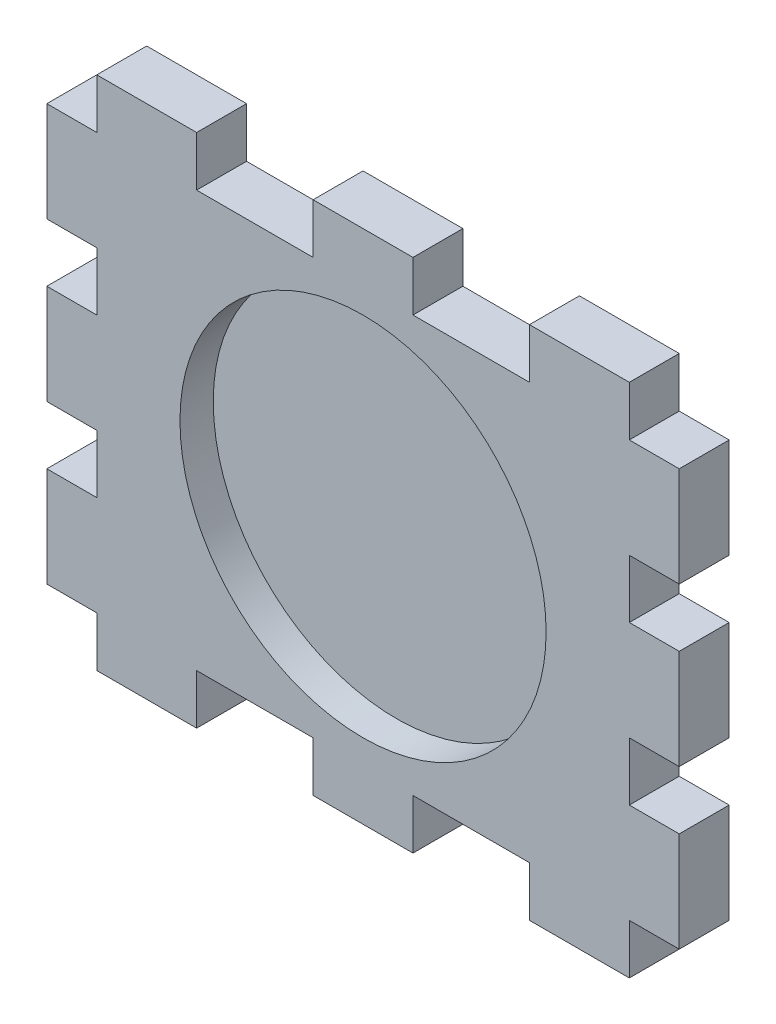
SolidWorks part; units mm, degrees
ref_plane "Front Plane" through (0, 0, 0) normal (0, 0, 1) x (1, 0, 0)
ref_plane "Top Plane" through (0, 0, 0) normal (0, 1, 0) x (1, 0, 0)
ref_plane "Right Plane" through (0, 0, 0) normal (1, 0, 0) x (0, 0, -1)
sketch "Sketch2" plane through (0, 0, 0) normal (0, 0, 1) x (1, 0, 0)
  line L0 (-35.0819, 0) -> (36.0241, 0) construction
  line L1 (-16, 12.5) -> (16, 12.5)
  line L2 (-16, 12.5) -> (-16, -12.5)
  line L3 (-16, -12.5) -> (16, -12.5)
  line L4 (16, 12.5) -> (16, -12.5)
  line L5 (0, 30.8422) -> (0, -34.9434) construction
  circle A0 centre (0, 0) radius 11
  point P9 (0, 0)
  dimension "D1" = 12.5
  dimension "D2" = 12.5
  dimension "D3" = 16
  dimension "D4" = 16
extrude "Boss-Extrude1" add sketch "Sketch2" along normal blind 3
sketch "Sketch3" plane through (0, 0, 0) normal (0, 0, -1) x (-1, 0, 0)
  circle A0 centre (0, 0) radius 11 construction
  circle A1 centre (0, 0) radius 11
extrude "Boss-Extrude2" add sketch "Sketch3" against normal blind 1
ref_plane "Plane1" through (0, 0, 0) normal (-1, 0, 0) x (0, 0, 1)
ref_plane "Plane2" through (0, 0, 0) normal (0, -1, 0) x (-1, 0, 0)
sketch "Sketch4" plane through (0, 0, 0) normal (0, 0, -1) x (-1, 0, 0)
  line L0 (0, -15.7256) -> (0, 15.7256) construction
  line L1 (-16, -12.5) -> (-10, -12.5)
  line L2 (-16, -12.5) -> (-16, -15.5)
  line L3 (-16, -15.5) -> (-10, -15.5)
  line L4 (-10, -12.5) -> (-10, -15.5)
  line L5 (10, -12.5) -> (10, -15.5)
  line L6 (16, -15.5) -> (10, -15.5)
  line L7 (16, -12.5) -> (16, -15.5)
  line L8 (16, -12.5) -> (10, -12.5)
  line L9 (16, -12.5) -> (-16, -12.5) construction
  line L10 (3, -12.5) -> (-3, -12.5)
  line L11 (3, -12.5) -> (3, -15.5)
  line L12 (3, -15.5) -> (-3, -15.5)
  line L13 (-3, -12.5) -> (-3, -15.5)
  line L14 (-12.4356, 0) -> (12.4356, 0) construction
  line L15 (-3, 12.5) -> (-3, 15.5)
  line L16 (3, 15.5) -> (-3, 15.5)
  line L17 (3, 12.5) -> (3, 15.5)
  line L18 (3, 12.5) -> (-3, 12.5)
  line L19 (16, 12.5) -> (10, 12.5)
  line L20 (16, 12.5) -> (16, 15.5)
  line L21 (16, 15.5) -> (10, 15.5)
  line L22 (10, 12.5) -> (10, 15.5)
  line L23 (-10, 12.5) -> (-10, 15.5)
  line L24 (-16, 15.5) -> (-10, 15.5)
  line L25 (-16, 12.5) -> (-16, 15.5)
  line L26 (-16, 12.5) -> (-10, 12.5)
  line L27 (-19, -12.5) -> (-19, -6.5)
  line L28 (-16, 12.5) -> (-19, 12.5)
  line L29 (-16, 12.5) -> (-16, 6.5)
  line L30 (-16, 6.5) -> (-19, 6.5)
  line L31 (-19, 12.5) -> (-19, 6.5)
  line L32 (-16, -6.5) -> (-19, -6.5)
  line L33 (-16, -12.5) -> (-16, -6.5)
  line L34 (-16, -12.5) -> (-19, -12.5)
  line L35 (-16, -12.5) -> (-16, 12.5) construction
  line L36 (-16, 3) -> (-19, 3)
  line L37 (-16, 3) -> (-16, -3)
  line L38 (-16, -3) -> (-19, -3)
  line L39 (-19, 3) -> (-19, -3)
  line L40 (19, 3) -> (19, -3)
  line L41 (16, -3) -> (19, -3)
  line L42 (16, 3) -> (16, -3)
  line L43 (16, 3) -> (19, 3)
  line L44 (16, -12.5) -> (19, -12.5)
  line L45 (16, -12.5) -> (16, -6.5)
  line L46 (16, -6.5) -> (19, -6.5)
  line L47 (19, 12.5) -> (19, 6.5)
  line L48 (16, 6.5) -> (19, 6.5)
  line L49 (16, 12.5) -> (16, 6.5)
  line L50 (16, 12.5) -> (19, 12.5)
  line L51 (19, -12.5) -> (19, -6.5)
  point P34 (-17.5, 6.5)
  point P44 (-17.5, 3)
  point P55 (-19, -15.5)
  point P56 (0, 0)
  point P60 (19, 15.5)
  line M5 (16, -12.5) -> (16, 12.5)
  line M6 (16, 12.5) -> (-16, 12.5)
  line M7 (-16, 12.5) -> (-16, -12.5)
  line M8 (-16, -12.5) -> (16, -12.5)
  dimension "D1" = 3
  dimension "D2" = 6
  dimension "D3" = 3
  dimension "D4" = 3
  dimension "D5" = 3
  dimension "D6" = 3
  dimension "D7" = 6
  dimension "D8" = 6
  dimension "D9" = 3
  dimension "D10" = 3
extrude "Boss-Extrude3" add sketch "Sketch4" against normal blind 3 contours L4 L2 L3 M8 | L34 L32 L27 M7 | L36 L39 L38 M7 | L28 L31 L30 M7 | L17 L16 L15 M6 | L22 L20 L21 M6 | L50 L48 L47 M5 | L43 L41 L40 M5 | L44 L51 L46 M5 | L7 L5 L6 M8 | L13 L12 L11 M8 | L25 L24 L23 L26
